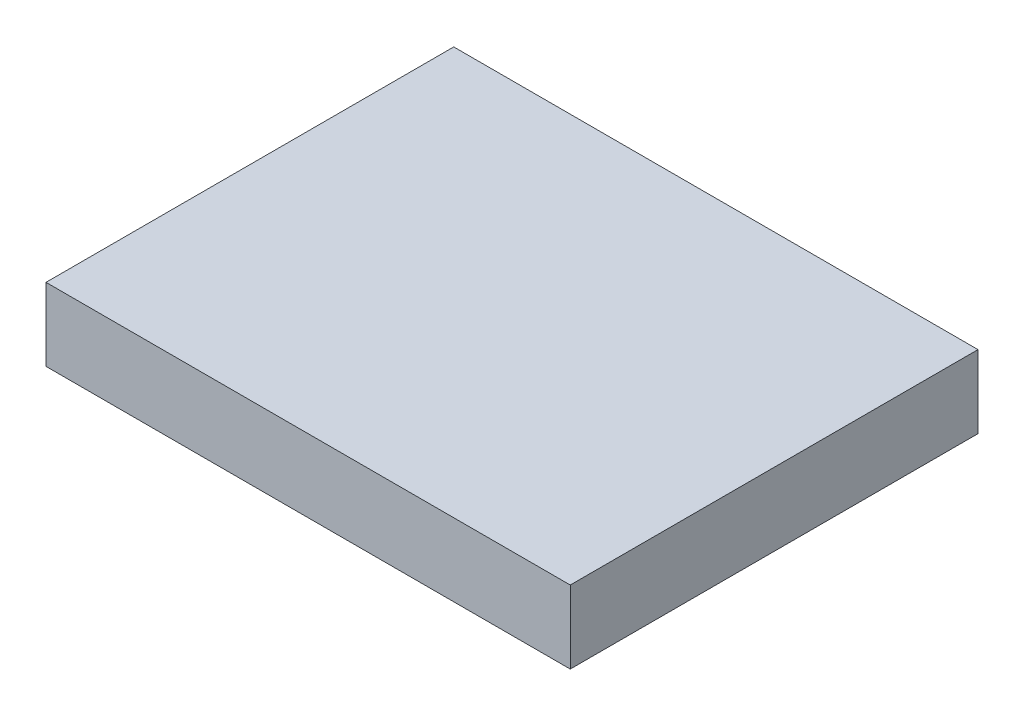
SolidWorks part; units mm, degrees
ref_plane "Front" through (0, 0, 0) normal (0, 0, 1) x (1, 0, 0)
ref_plane "Top" through (0, 0, 0) normal (0, 1, 0) x (1, 0, 0)
ref_plane "Right" through (0, 0, 0) normal (1, 0, 0) x (0, 0, -1)
sketch "Sketch1" plane through (0, 0, 0) normal (0, 1, 0) x (1, 0, 0)
  line L1 (0, 0) -> (21.6, 0)
  line L2 (0, 0) -> (0, -16.8)
  line L3 (0, -16.8) -> (21.6, -16.8)
  line L4 (21.6, 0) -> (21.6, -16.8)
  dimension "D1" = 16.8
  dimension "D2" = 21.6
extrude "Boss-Extrude1" add sketch "Sketch1" along normal blind 3
